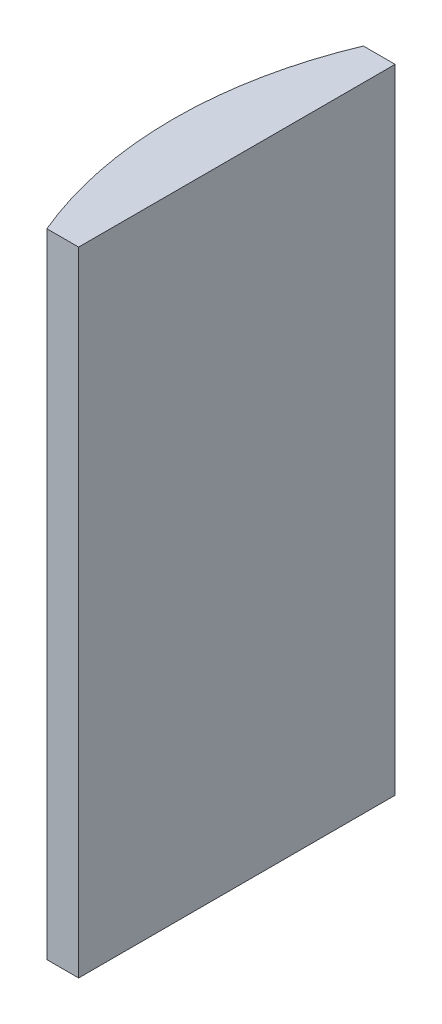
SolidWorks part; units mm, degrees
ref_plane "前视基准面" through (0, 0, 0) normal (0, 0, 1) x (1, 0, 0)
ref_plane "上视基准面" through (0, 0, 0) normal (0, 1, 0) x (1, 0, 0)
ref_plane "右视基准面" through (0, 0, 0) normal (1, 0, 0) x (0, 0, -1)
sketch "草图1" plane through (0, 0, 0) normal (0, 1, 0) x (1, 0, 0)
  line L0 (10.7432, 0) -> (-607.0701, 0) construction
  line L1 (-19.4822, 10) -> (-17.4748, 10)
  line L2 (-19.4822, -10) -> (-17.4748, -10)
  line L3 (-17.4748, 10) -> (-17.4748, -10)
  arc A0 (-19.4822, 10) -> (-19.4822, -10) centre (4.3552, 0) ccw
  point P19 (-21.4948, 0)
  point P20 (-17.4748, 0)
  dimension "D2" = 10
  dimension "D3" = 25.85
  dimension "D4" = 4.02
  dimension "D1" = 10
extrude "凸台-拉伸1" add sketch "草图1" along normal blind 40
